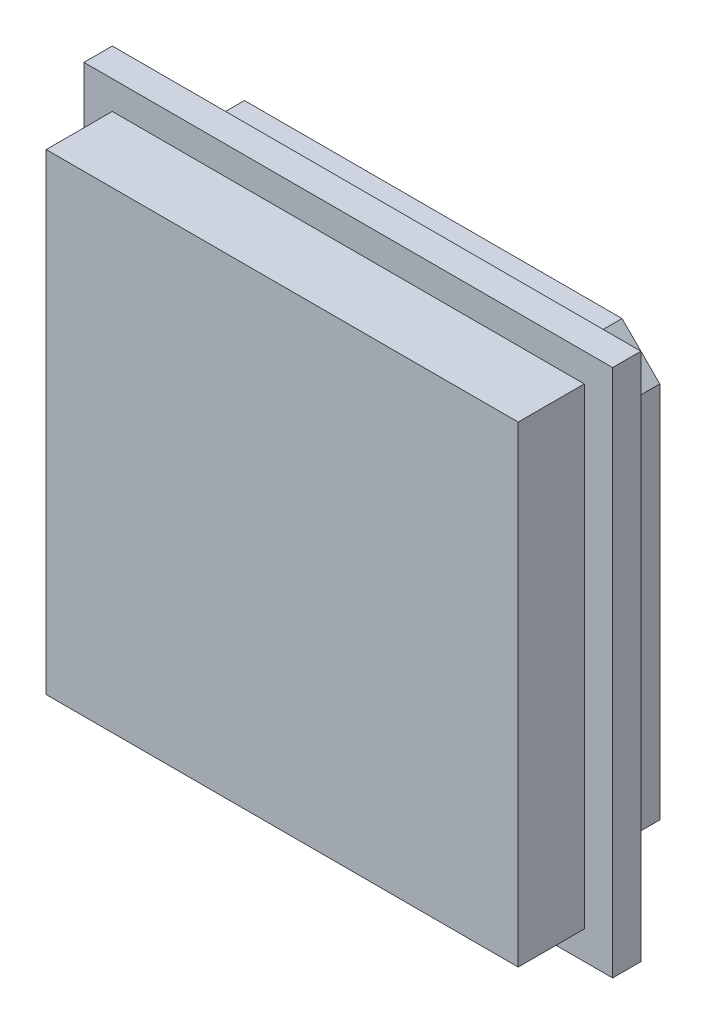
SolidWorks part; units mm, degrees
ref_plane "Front Plane" through (0, 0, 0) normal (0, 0, 1) x (1, 0, 0)
ref_plane "Top Plane" through (0, 0, 0) normal (0, 1, 0) x (1, 0, 0)
ref_plane "Right Plane" through (0, 0, 0) normal (1, 0, 0) x (0, 0, -1)
sketch "Sketch1" plane through (0, 0, 0) normal (0, 0, 1) x (1, 0, 0)
  line L0 (-198.0073, 0) -> (-198.0073, 166) construction
  line L1 (-166.0073, 36) -> (-186.0073, 36)
  line L2 (-164.0073, 34) -> (-164.0073, 14)
  line L3 (-166.0073, 12) -> (-186.0073, 12)
  line L4 (-188.0073, 34) -> (-188.0073, 14)
  line L5 (-148.0073, 0) -> (-193.0073, 0) construction
  line L6 (-186.0073, 36) -> (-188.0073, 34)
  line L7 (-164.0073, 34) -> (-166.0073, 36)
  line L8 (-164.0073, 14) -> (-166.0073, 12)
  line L9 (-186.0073, 12) -> (-188.0073, 14)
  point P0 (-164.0073, 36)
  point P1 (-188.0073, 12)
  point P2 (-164.0073, 12)
  point P3 (-188.0073, 36)
  dimension "D1" = 24
  dimension "D2" = 24
  dimension "D3" = 10
  dimension "D4" = 12
extrude "Boss-Extrude1" add sketch "Sketch1" along normal blind 3
sketch "Sketch2" plane through (0, 0, 3) normal (0, 0, 1) x (1, 0, 0)
  line L0 (-166.0073, 36) -> (-186.0073, 36) construction
  line L1 (-162.0073, 38) -> (-190.0073, 38)
  line L2 (-162.0073, 38) -> (-162.0073, 10)
  line L3 (-162.0073, 10) -> (-190.0073, 10)
  line L4 (-190.0073, 38) -> (-190.0073, 10)
  line L5 (-186.0073, 12) -> (-166.0073, 12) construction
  line L6 (-164.0073, 14) -> (-164.0073, 34) construction
  line L7 (-188.0073, 34) -> (-188.0073, 14) construction
  dimension "D1" = 2
  dimension "D2" = 2
  dimension "D3" = 2
  dimension "D4" = 2
extrude "Boss-Extrude2" add sketch "Sketch2" along normal blind 1.5
sketch "Sketch3" plane through (0, 0, 4.5) normal (0, 0, 1) x (1, 0, 0)
  line L0 (-162.0073, 24) -> (-190.0073, 24) construction
  line L1 (-163.5073, 36.5) -> (-188.5073, 36.5)
  line L2 (-163.5073, 36.5) -> (-163.5073, 11.5)
  line L3 (-163.5073, 11.5) -> (-188.5073, 11.5)
  line L4 (-188.5073, 36.5) -> (-188.5073, 11.5)
  line L5 (-162.0073, 10) -> (-162.0073, 38) construction
  line L6 (-190.0073, 38) -> (-190.0073, 10) construction
  line L7 (-176.0073, 38) -> (-176.0073, 10) construction
  line L8 (-162.0073, 38) -> (-190.0073, 38) construction
  line L9 (-190.0073, 10) -> (-162.0073, 10) construction
  dimension "D1" = 25
  dimension "D2" = 25
  dimension "D3" = 12.5
  dimension "D4" = 12.5
extrude "Boss-Extrude3" add sketch "Sketch3" along normal blind 3.5
